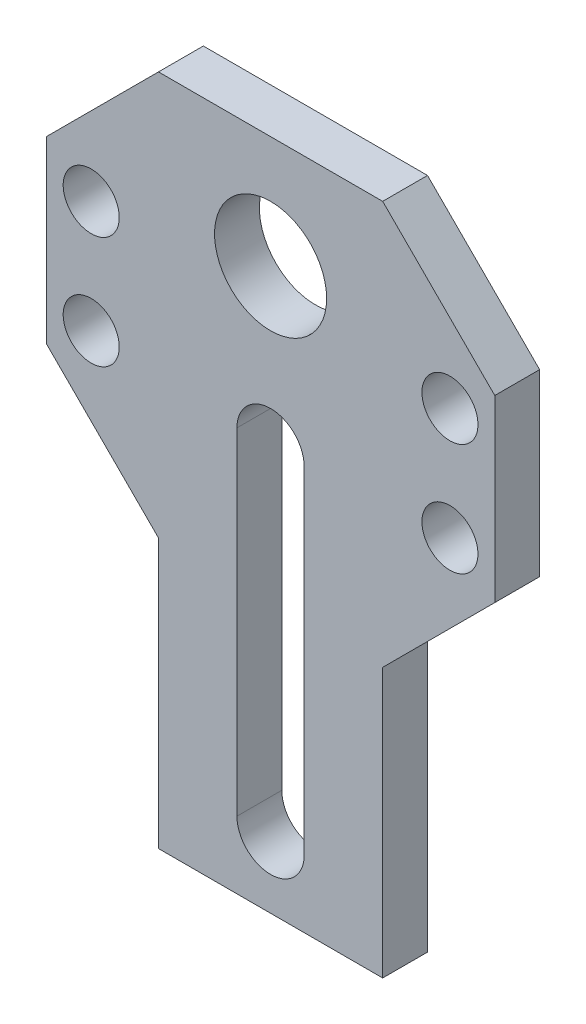
SolidWorks part; units mm, degrees
ref_plane "Front Plane" through (0, 0, 0) normal (0, 0, 1) x (1, 0, 0)
ref_plane "Top Plane" through (0, 0, 0) normal (0, 1, 0) x (1, 0, 0)
ref_plane "Right Plane" through (0, 0, 0) normal (1, 0, 0) x (0, 0, -1)
sketch "Sketch1" plane through (0, 0, 0) normal (0, 0, 1) x (1, 0, 0)
  line L1 (0, 0) -> (10, 0)
  line L2 (0, 0) -> (0, 30)
  line L3 (0, 30) -> (10, 30)
  line L4 (10, 0) -> (10, 30)
  dimension "D1" = 10
  dimension "D2" = 30
extrude "Boss-Extrude1" add sketch "Sketch1" along normal blind 2
sketch "Sketch2" plane through (0, 0, 2) normal (0, 0, 1) x (1, 0, 0)
  line L0 (10, 30) -> (0, 30) construction
  circle A0 centre (5, 25) radius 2.5
  dimension "D1" = 5
  dimension "D2" = 5
extrude "Cut-Extrude1" cut sketch "Sketch2" against normal blind 2
sketch "Sketch3" plane through (0, 0, 2) normal (0, 0, 1) x (1, 0, 0)
  line L0 (5, 3) -> (5, 18) construction
  line L1 (3.5, 3) -> (3.5, 18)
  line L2 (6.5, 3) -> (6.5, 18)
  line L3 (0, 0) -> (10, 0) construction
  arc A0 (3.5, 3) -> (6.5, 3) centre (5, 3) ccw
  arc A1 (6.5, 18) -> (3.5, 18) centre (5, 18) ccw
  point P2 (5, 10.5)
  dimension "D2" = 1.5
  dimension "D1" = 3
  dimension "D3" = 15
extrude "Cut-Extrude2" cut sketch "Sketch3" against normal blind 2
sketch "Sketch4" plane through (0, 0, 2) normal (0, 0, 1) x (1, 0, 0)
  line L0 (0, 30) -> (-5, 25)
  line L1 (-5, 25) -> (-5, 17)
  line L2 (-5, 17) -> (0, 12)
  line L3 (0, 30) -> (0, 0) construction
  line L4 (0, 30) -> (0, 12)
  line L5 (5, 30) -> (5, 25.4182) construction
  line L6 (10, 30) -> (0, 30) construction
  line L7 (10, 30) -> (15, 25)
  line L8 (15, 25) -> (15, 17)
  line L9 (15, 17) -> (10, 12)
  line L10 (10, 30) -> (10, 12)
  dimension "D1" = 45
  dimension "D2" = 45
  dimension "D3" = 5
  dimension "D4" = 8
extrude "Boss-Extrude2" add sketch "Sketch4" against normal blind 2
sketch "Sketch5" plane through (0, 0, 2) normal (0, 0, 1) x (1, 0, 0)
  line L0 (-5, 25) -> (-5, 17) construction
  line L1 (5, 27.5) -> (5, 22.5) construction
  circle A0 centre (-3, 23.5) radius 1.25
  circle A1 centre (-3, 18.5) radius 1.25
  circle A2 centre (5, 25) radius 2.5 construction
  circle A3 centre (13, 18.5) radius 1.25
  circle A4 centre (13, 23.5) radius 1.25
  dimension "D1" = 2.5
  dimension "D2" = 2.5
  dimension "D3" = 5
  dimension "D4" = 1.5
  dimension "D5" = 2
extrude "Cut-Extrude3" cut sketch "Sketch5" against normal blind 2
